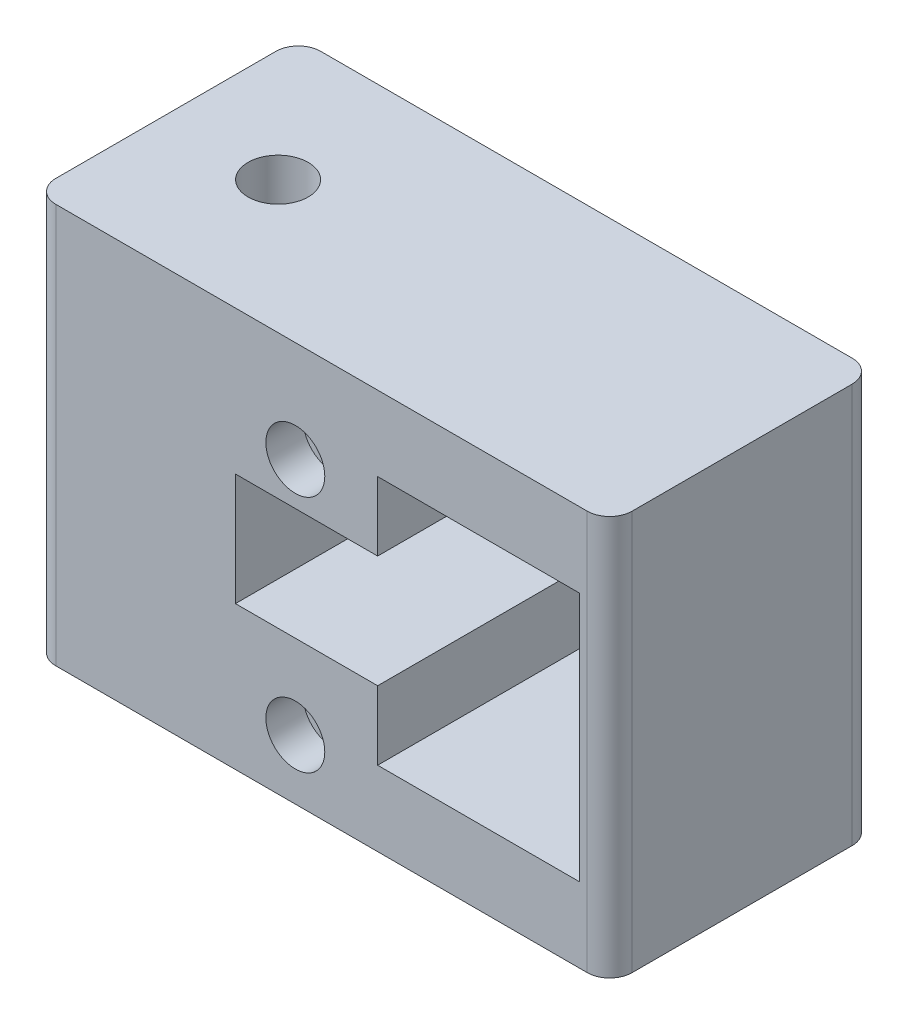
SolidWorks part; units mm, degrees
ref_plane "Front Plane" through (0, 0, 0) normal (0, 0, 1) x (1, 0, 0)
ref_plane "Top Plane" through (0, 0, 0) normal (0, 1, 0) x (1, 0, 0)
ref_plane "Right Plane" through (0, 0, 0) normal (1, 0, 0) x (0, 0, -1)
sketch "Sketch1" plane through (0, 0, 0) normal (0, 0, 1) x (1, 0, 0)
  line L0 (7.62, 30.734) -> (7.62, 42.418)
  line L1 (7.62, 0) -> (41.91, 0)
  line L2 (7.62, 0) -> (7.62, 11.684)
  line L3 (7.62, 42.418) -> (41.91, 42.418)
  line L4 (41.91, 0) -> (41.91, 42.418)
  line L5 (-50.8, 55.118) -> (46.99, 55.118)
  line L6 (-50.8, 55.118) -> (-50.8, -12.7)
  line L7 (-50.8, -12.7) -> (46.99, -12.7)
  line L8 (46.99, 55.118) -> (46.99, -12.7)
  line L9 (7.62, 30.734) -> (-16.51, 30.734)
  line L11 (7.62, 11.684) -> (-16.51, 11.684)
  line L12 (-16.51, 30.734) -> (-16.51, 11.684)
  dimension "D1" = 42.418
  dimension "D2" = 34.29
  dimension "D3" = 5.08
  dimension "D4" = 24.13
  dimension "D5" = 19.05
  dimension "D6" = 11.684
  dimension "D7" = 97.79
  dimension "D8" = 12.7
  dimension "D9" = 12.7
  dimension "D10" = 7.62
extrude "Boss-Extrude1" add sketch "Sketch1" along normal blind 42.418
sketch "Sketch2" plane through (0, 0, 0) normal (0, 0, -1) x (-1, 0, 0)
  line L1 (-46.99, 55.118) -> (50.8, 55.118)
  line L2 (-46.99, 55.118) -> (-46.99, -12.7)
  line L3 (-46.99, -12.7) -> (50.8, -12.7)
  line L4 (50.8, 55.118) -> (50.8, -12.7)
extrude "Boss-Extrude2" add sketch "Sketch2" along normal blind 2.54
sketch "Sketch3" plane through (0, -12.7, 0) normal (0, -1, 0) x (1, 0, 0)
  line L0 (-50.8, 42.418) -> (-50.8, -2.54) construction
  line L1 (-50.8, 42.418) -> (46.99, 42.418) construction
  circle A0 centre (-31.75, 19.939) radius 4.064
  dimension "D1" = 8.128
  dimension "D2" = 19.05
  dimension "D3" = 22.479
extrude "Cut-Extrude1" cut sketch "Sketch3" against normal through all
sketch "Sketch4" plane through (0, 0, 42.418) normal (0, 0, 1) x (1, 0, 0)
  line L0 (-50.8, -12.7) -> (46.99, -12.7) construction
  line L2 (46.99, -12.7) -> (46.99, 55.118) construction
  circle A0 centre (-6.35, 37.96) radius 5
  circle A1 centre (-6.35, -2.54) radius 5
  dimension "D1" = 10
  dimension "D2" = 10
  dimension "D3" = 40.5
  dimension "D4" = 10.16
  dimension "D5" = 53.34
  dimension "D6" = 53.34
extrude "Cut-Extrude2" cut sketch "Sketch4" against normal blind 6.35
sketch "Sketch5" plane through (0, 55.118, 0) normal (0, 1, 0) x (1, 0, 0)
  circle A0 centre (-31.75, -19.939) radius 5.1
  dimension "D1" = 10.2
extrude "Cut-Extrude3" cut sketch "Sketch5" against normal blind 15.24
fillet "Fillet1" radius 3.81 4 edges at (-50.8, 21.209, -2.54) (-50.8, 21.209, 42.418) (46.99, 21.209, -2.54) (46.99, 21.209, 42.418)
